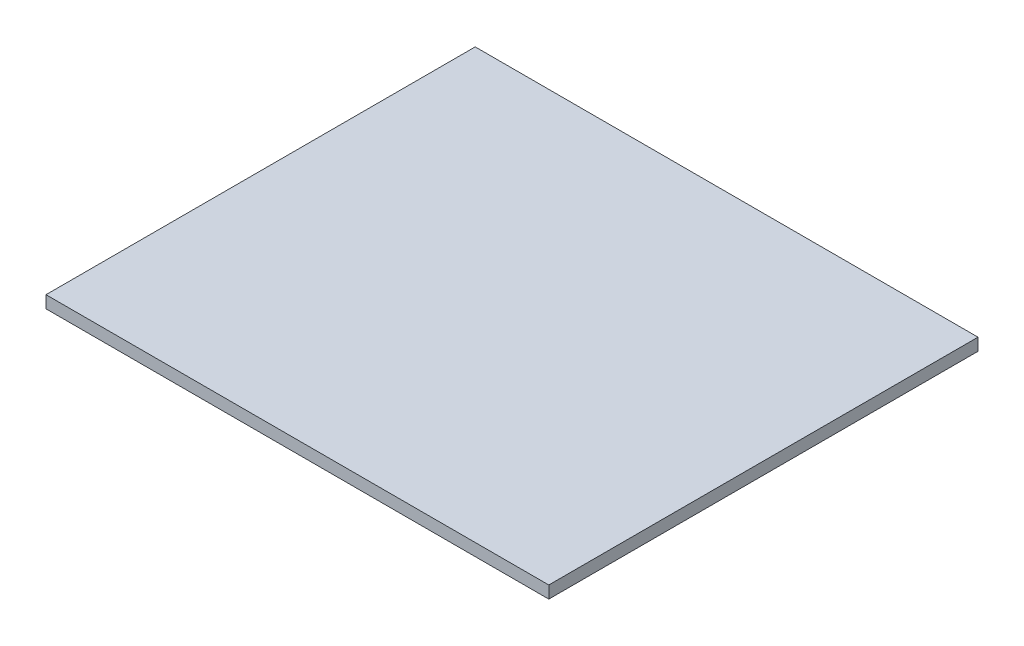
SolidWorks part; units mm, degrees
ref_plane "Front Plane" through (0, 0, 0) normal (0, 0, 1) x (1, 0, 0)
ref_plane "Top Plane" through (0, 0, 0) normal (0, 1, 0) x (1, 0, 0)
ref_plane "Right Plane" through (0, 0, 0) normal (1, 0, 0) x (0, 0, -1)
sketch "Sketch1" plane through (0, 0, 0) normal (0, 1, 0) x (1, 0, 0)
  line L5 (-61.5, -52.5) -> (61.5, -52.5)
  line L6 (-61.5, -52.5) -> (-61.5, 52.5)
  line L7 (-61.5, 52.5) -> (61.5, 52.5)
  line L8 (61.5, -52.5) -> (61.5, 52.5)
  line L10 (0, 52.5) -> (0, -52.5) construction
  line L18 (-61.5, 0) -> (61.5, 0) construction
  point P0 (0, 0)
  dimension "D1" = 123
  dimension "D2" = 105
extrude "BasePlate" add sketch "Sketch1" along normal blind 3
equation "\"BoltD\"=2mm"
equation "\"BoltHatD\"=3.2mm"
equation "\"NutShortSide\"=4mm"
equation "\"NutLongSide\"=4.5mm"
equation "\"SmallScrewD\"=1.2mm"
equation "\"SmallScrewHatD\"=2mm"
equation "\"TubeOuterD\"=1.2mm"
equation "\"TubeClipW\"=1.5mm"
equation "\"TubeClipH\"=1.5mm"
equation "\"TubeClipLock_SideL\"=1.5mm"
equation "\"TubeClipLock_W\"=0.7mm"
equation "\"BasicPulleyD\"=15mm"
equation "\"GrooveDepth\"=0.7mm"
equation "\"Cable1D\"=0.4mm"
equation "\"Cable2D\"=0.3mm"
equation "\"BallBearingInnerD\"=2mm"
equation "\"BallBearingOuterD\"=4mm"
equation "\"BallBearingThickness\"=2mm"
equation "\"BearingCapD\"=12mm"
equation "\"HumerusL\"=37.2mm"
equation "\"HumerusElbowSidePulleyD\"=10mm"
equation "\"RadiusL\"=68.1mm"
equation "\"Finger1L\"=120mm"
equation "\"Finger2L\"=100mm"
equation "\"Finger3L\"=80mm"
equation "\"ElbowExtendedAngle\"=140deg"
equation "\"ElbowFlexedAngle\"=38deg"
equation "\"Digit5ExtendedAngle\"=80deg"
equation "\"Digit5FlexedAngle\"=24deg"
equation "\"Digit4ExtendedAngle\"=108deg"
equation "\"Digit4FlexedAngle\"=34deg"
equation "\"Digit3ExtendedAngle\"=145deg"
equation "\"Digit3FlexedAngle\"=44deg"
equation "\"KST_ServoBoltShelfHeight\"=21.1mm"
equation "\"KST_ServoLength\"=23mm"
equation "\"KST_ServoWidth\"=12mm"
equation "\"KST_ServoBoltHole2HoleLength\"=28mm"
equation "\"KST_ServoBoltHole2ShaftDist\"=8.3mm"
equation "\"KST_ServoBoltHole2HoleWidth\"=7mm"
equation "\"KST_ServoHeight\"=27.5mm"
equation "\"KST_ServoShaftHeight\"=3.5mm"
equation "\"KST_ServoShaftD\"=4.25mm"
equation "\"KST_ServoShaftToothL\"=0.345mm"
equation "\"KST_ServoShaftToothAngle\"=60deg"
equation "\"KST_ServoShaftToothTipWidth\"=0.18mm"
equation "\"KST_ServoShaftToothFilletR\"=0.1mm"
equation "\"KST_ServoShaftToothN\"=25"
equation "\"KST_ServoShaftBoltD\"=2mm"
equation "\"KST_ServoShaftBoltHatD\"=5mm"
equation "\"XL330_M077_T_Length\"=34mm"
equation "\"XL330_M077_T_Width\"=20mm"
equation "\"XL330_M077_T_Height\"=23mm"
equation "\"XL330_M077_T_BoltHole2HoleLength\"=30mm"
equation "\"XL330_M077_T_BoltHole2HoleWidth\"=16mm"
equation "\"XL330_M077_T_BoltHole2ShaftDist\"=7.5mm"
equation "\"XL330_M077_T_HornHeight\"=3mm"
equation "\"XL330_M077_T_HornBoltD\"=2mm"
equation "\"XL330_M077_T_HornBoltHatD\"=5.6mm"
equation "\"XL330_M077_T_HornD\"=16mm"
equation "\"XL330_M077_T_HornScrewHoleCircleD\"=12mm"
equation "\"XL330_M077_T_BoltD\"=1.6mm"
equation "\"XL330_M077_T_FrameBoltD\"=1.6mm"
equation "\"XL330_M077_T_FrameNutShortSide\"=2.5mm"
equation "\"XL330_M077_T_FrameNutLongSide\"=3mm"
equation "\"XL330_M077_T_HornScrewD\"=1.9mm"
equation "\"XL330_M077_T_HornScrewHatD\"=3.3mm"
